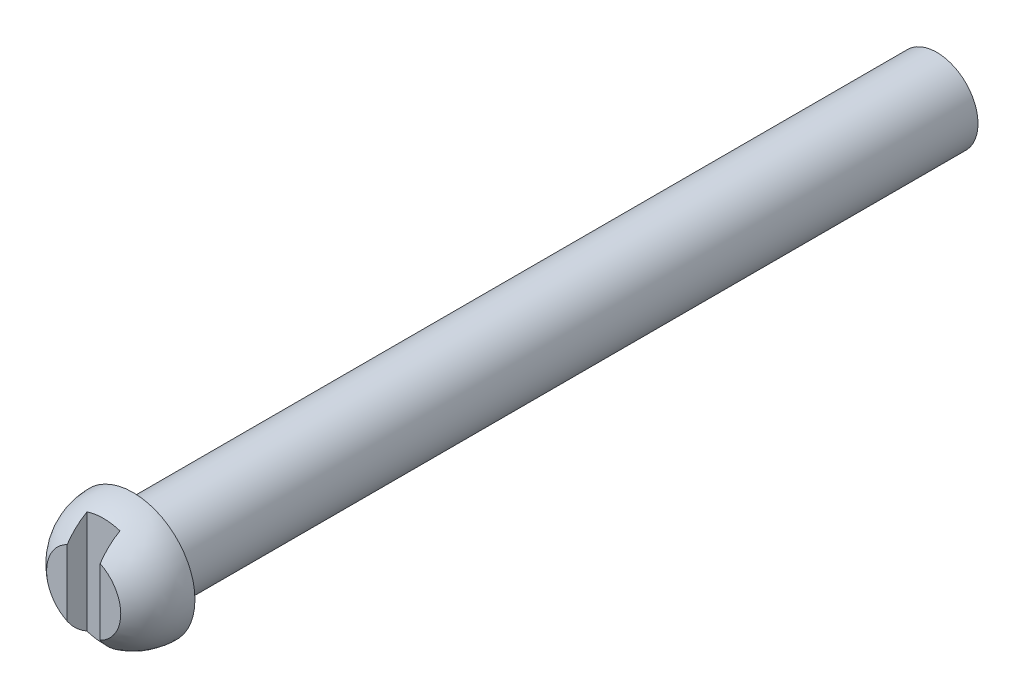
SolidWorks part; units mm, degrees
ref_plane "Front Plane" through (0, 0, 0) normal (0, 0, 1) x (1, 0, 0)
ref_plane "Top Plane" through (0, 0, 0) normal (0, 1, 0) x (1, 0, 0)
ref_plane "Right Plane" through (0, 0, 0) normal (1, 0, 0) x (0, 0, -1)
sketch "Sketch1" plane through (0, 0, 0) normal (0, 0, 1) x (1, 0, 0)
  circle A0 centre (0, 0) radius 3.175
  dimension "D1" = 6.35
extrude "Boss-Extrude1" add sketch "Sketch1" along normal blind 15.875 and the other way blind 46.0375
sketch "Sketch2" plane through (0, 0, 15.875) normal (0, 0, 1) x (1, 0, 0)
  line L0 (0, -4.7625) -> (0, 4.7625)
  line L1 (0, -4.7625) -> (-3.103, -4.7625) construction
  arc A0 (0, -4.7625) -> (0, 4.7625) centre (0, 0) ccw
  dimension "D1" = 9.525
revolve "Revolve1" add sketch "Sketch2" angle 180 about L0
ref_plane "Plane1" through (2.54, 0, 0) normal (1, 0, 0) x (0, 0, -1)
sketch "Sketch3" plane through (2.54, 0, 0) normal (1, 0, 0) x (0, 0, -1)
  line L0 (-15.875, -2.8575) -> (-15.875, 5.715) construction
  line L1 (-22.225, 4.7625) -> (-19.685, 4.7625)
  line L2 (-22.225, 4.7625) -> (-22.225, -7.9375)
  line L3 (-22.225, -7.9375) -> (-19.685, -7.9375)
  line L4 (-19.685, 4.7625) -> (-19.685, -7.9375)
  dimension "D1" = 3.81
  dimension "D2" = 2.54
  dimension "D3" = 0
  dimension "D4" = 12.7
extrude "Cut-Extrude1" cut sketch "Sketch3" against normal blind 9.398 and the other way blind 8.382
sketch "Sketch4" plane through (0, 0, 19.685) normal (0, 0, 1) x (1, 0, 0)
  line L0 (2.8575, 0) -> (1.27, 0) construction
  line L1 (1.27, 5.6131) -> (-1.27, 5.6131)
  line L2 (1.27, 5.6131) -> (1.27, -7.1989)
  line L3 (1.27, -7.1989) -> (-1.27, -7.1989)
  line L4 (-1.27, 5.6131) -> (-1.27, -7.1989)
  line L5 (-1.27, 0) -> (-2.8575, 0) construction
  circle A0 centre (0, 0) radius 2.8575 construction
  dimension "D1" = 2.54
extrude "Cut-Extrude2" cut sketch "Sketch4" against normal blind 1.524
sketch "Sketch5" plane through (0, 0, -46.0375) normal (0, 0, -1) x (-1, 0, 0)
  circle A0 centre (0, 0) radius 3.175
